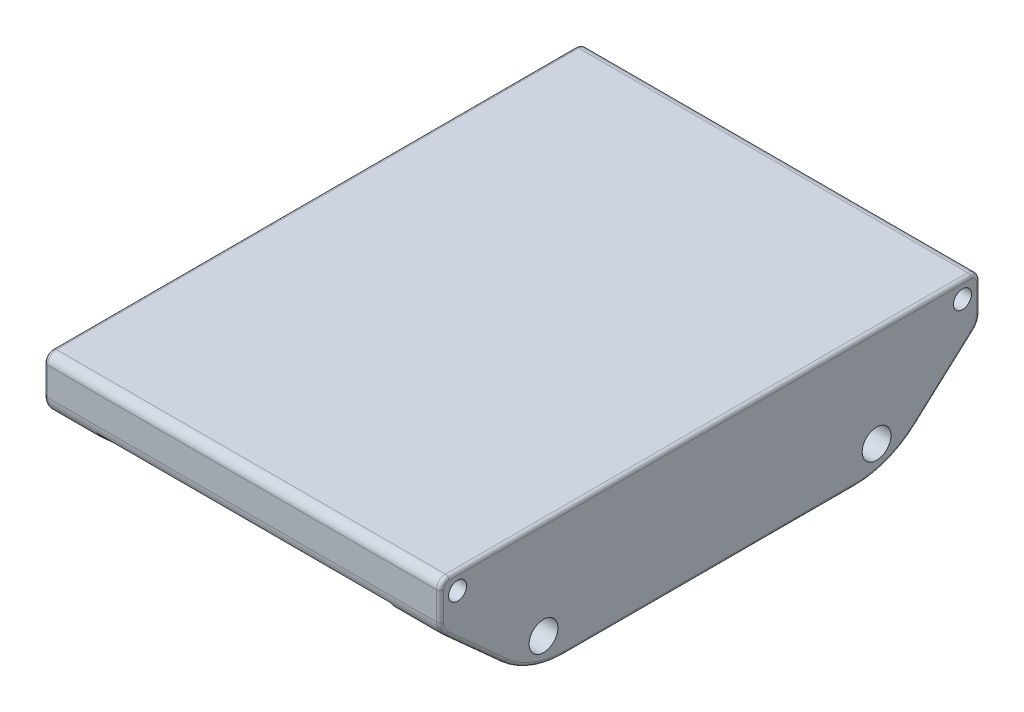
SolidWorks part; units mm, degrees
material "1023 Carbon Steel Sheet (SS)"
ref_plane "Front Plane" through (0, 0, 0) normal (0, 0, 1) x (1, 0, 0)
ref_plane "Top Plane" through (0, 0, 0) normal (0, 1, 0) x (1, 0, 0)
ref_plane "Right Plane" through (0, 0, 0) normal (1, 0, 0) x (0, 0, -1)
sketch "Sketch1" plane through (0, 0, 0) normal (0, 1, 0) x (1, 0, 0)
  line L0 (-110, -150) -> (110, -150)
  line L1 (-110, -150) -> (-110, 150)
  line L2 (-110, 150) -> (110, 150)
  line L3 (110, -150) -> (110, 150)
  dimension "D1" = 220
  dimension "D2" = 300
extrude "Boss-Extrude1" add sketch "Sketch1" along normal blind 70
sketch "Sketch2" plane through (-110, 0, 0) normal (-1, 0, 0) x (0, 0, 1)
  line L0 (-150, 70) -> (-150, 15) construction
  line L1 (150, 15) -> (127.5, 15) construction
  line L3 (150, 70) -> (150, 0) construction
  line L4 (-150, 70) -> (-150, 0) construction
  line L5 (127.5, 15) -> (57.5, 15) construction
  line L6 (-127.5, 15) -> (-57.5, 15) construction
  line L7 (-57.5, 15) -> (57.5, 15) construction
  line L8 (-92.5, 15) -> (-150, 70) construction
  line L9 (92.5, 15) -> (150, 70) construction
  line L10 (-127.5, 15) -> (-150, 15)
  circle A0 centre (-92.5, 15) radius 35
  circle A1 centre (92.5, 15) radius 35
  circle A3 centre (-140.1944, 60.6207) radius 21
  circle A4 centre (140.1944, 60.6207) radius 21
  circle A5 centre (-140.1944, 60.6207) radius 5
  circle A6 centre (-92.5, 15) radius 8
  circle A8 centre (92.5, 15) radius 8
  circle A9 centre (140.1944, 60.6207) radius 5
  dimension "D7" = 66
  dimension "D8" = 66
  dimension "D9" = 10
  dimension "D10" = 42
  dimension "D11" = 16
  dimension "D13" = 16
  dimension "D14" = 10
  dimension "D15" = 42
  dimension "D1" = 55
  dimension "D2" = 22.5
  dimension "D3" = 70
  dimension "D4" = 22.5
  dimension "D5" = 70
extrude "Cut-Extrude1" cut sketch "Sketch2" against normal through all
chamfer "Chamfer1" distance 50 angle 42 2 edges at (0, 0, 150) (0, 0, -150)
fillet "Fillet1" radius 5 2 edges at (0, 70, -150) (0, 70, 150)
fillet "Fillet2" radius 10 2 edges at (0, 45.0202, -150) (0, 45.0202, 150)
fillet "Fillet3" radius 50 2 edges at (0, 0, -100) (0, 0, 100)
sketch "Sketch3" plane through (0, 0, 0) normal (0, 0, 1) x (1, 0, 0)
  line L0 (110, 0) -> (-110, 0) construction
  line L1 (80, 45) -> (-80, 45)
  line L2 (80, 45) -> (80, 0)
  line L3 (80, 0) -> (-80, 0)
  line L4 (-80, 45) -> (-80, 0)
  line L5 (110, 42.041) -> (110, 12.8428) construction
  line L6 (-110, 12.8428) -> (-110, 42.041) construction
  line L7 (-110, 70) -> (110, 70) construction
  point P10 (-110, 27.4419)
  dimension "D1" = 30
  dimension "D2" = 30
  dimension "D3" = 25
extrude "Cut-Extrude2" cut sketch "Sketch3" against normal through all both and the other way through all
fillet "Fillet4" radius 2 14 edges at (80, 27.4419, -130.4773) (80, 3.321, -98.7252) (80, 0, 0) (80, 3.321, 98.7252) (-80, 27.4419, -130.4773) (-80, 3.321, -98.7252) (-80, 0, 0) (-80, 3.321, 98.7252) (80, 27.4419, 130.4773) (-80, 27.4419, 130.4773) (80, 43.4149, -147.9565) (80, 43.4149, 147.9565) (-80, 43.4149, 147.9565) (-80, 43.4149, -147.9565)
fillet "Fillet5" radius 2 24 edges at (110, 68.5355, 148.5355) (110, 57.2362, 150) (110, 45.4051, 149.1355) (110, 27.4419, 130.4773) (110, 3.321, 98.7252) (110, 0, 0) (110, 3.321, -98.7252) (110, 27.4419, -130.4773) (110, 45.4051, -149.1355) (110, 57.2362, -150) (110, 68.5355, -148.5355) (-110, 68.5355, -148.5355) (-110, 57.2362, -150) (-110, 45.4051, -149.1355) (-110, 27.4419, -130.4773) (-110, 3.321, -98.7252) (-110, 0, 0) (-110, 3.321, 98.7252) (-110, 27.4419, 130.4773) (-110, 45.4051, 149.1355) (-110, 57.2362, 150) (-110, 68.5355, 148.5355) (110, 70, 0) (-110, 70, 0)
